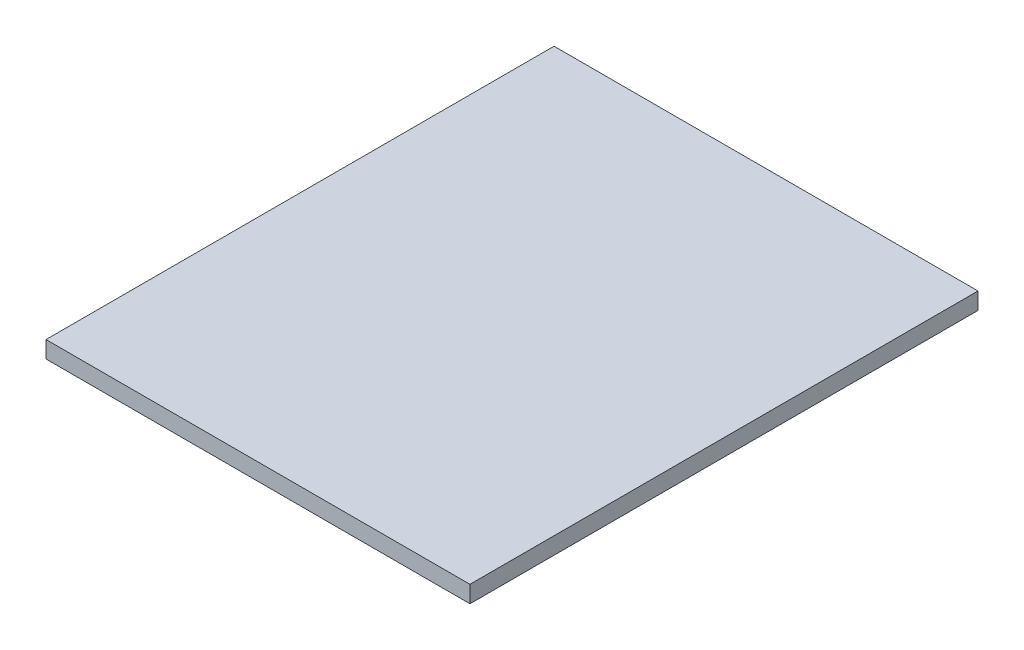
SolidWorks part; units mm, degrees
material "Pine"
ref_plane "Front Plane" through (0, 0, 0) normal (0, 0, 1) x (1, 0, 0)
ref_plane "Top Plane" through (0, 0, 0) normal (0, 1, 0) x (1, 0, 0)
ref_plane "Right Plane" through (0, 0, 0) normal (1, 0, 0) x (0, 0, -1)
sketch "Sketch1" plane through (0, 0, 0) normal (0, 1, 0) x (1, 0, 0)
  line L1 (-345.9953, 327.2158) -> (132.5047, 327.2158)
  line L2 (-345.9953, 327.2158) -> (-345.9953, -246.2222)
  line L3 (-345.9953, -246.2222) -> (132.5047, -246.2222)
  line L4 (132.5047, 327.2158) -> (132.5047, -246.2222)
  line L5 (-345.9953, 327.2158) -> (132.5047, -246.2222) construction
  line L6 (-345.9953, -246.2222) -> (132.5047, 327.2158) construction
  point P0 (0, 0)
  point P1 (-106.7453, 40.4968)
  point P6 (0, 0)
  point P7 (132.5047, -246.2222)
extrude "Boss-Extrude1" add sketch "Sketch1" along normal blind 19.05
